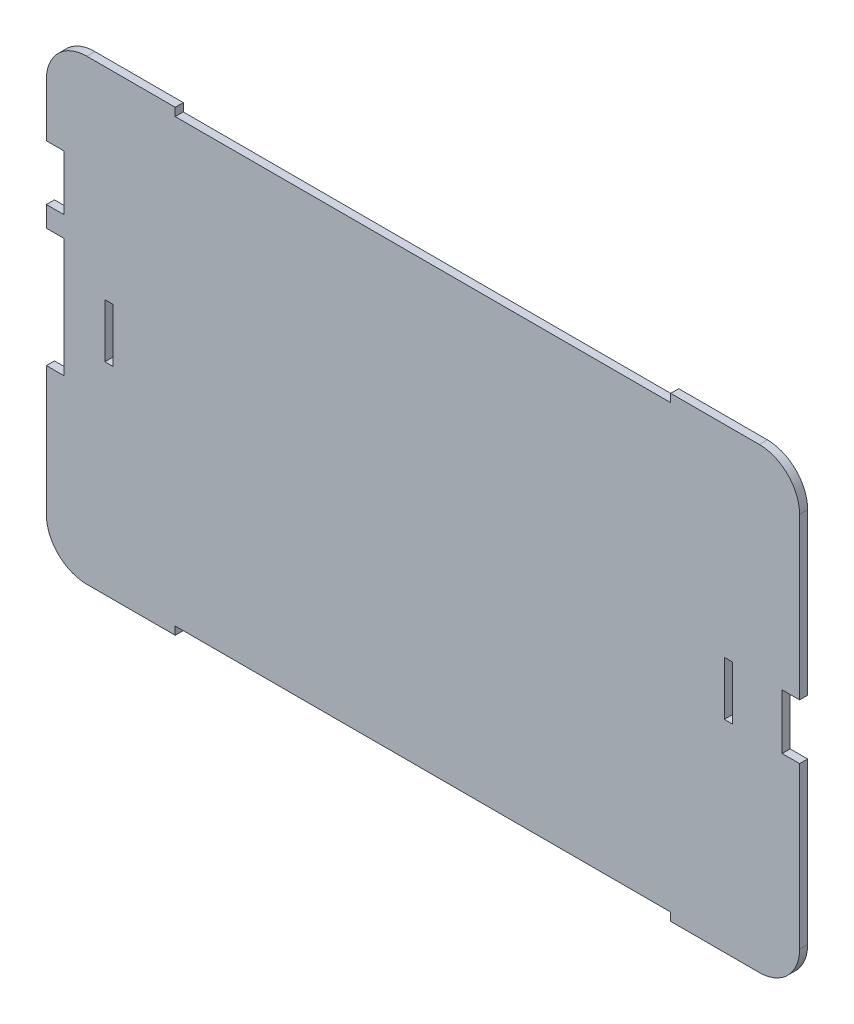
SolidWorks part; units mm, degrees
ref_plane "Alzado" through (0, 0, 0) normal (0, 0, 1) x (1, 0, 0)
ref_plane "Planta" through (0, 0, 0) normal (0, 1, 0) x (1, 0, 0)
ref_plane "Vista lateral" through (0, 0, 0) normal (1, 0, 0) x (0, 0, -1)
sketch "Croquis1" plane through (0, 0, 0) normal (0, 0, 1) x (1, 0, 0)
  line L0 (-207.3448, 3) -> (-174.4448, 3)
  line L1 (-174.4448, 3) -> (-174.4448, 0)
  line L2 (-174.4448, 0) -> (9.7552, 0)
  line L3 (9.7552, 0) -> (9.7552, 3)
  line L4 (9.7552, 3) -> (42.6552, 3)
  line L5 (-207.3448, -167) -> (-174.4448, -167)
  line L6 (-174.4448, -167) -> (-174.4448, -164)
  line L7 (-174.4448, -164) -> (9.7552, -164)
  line L8 (9.7552, -164) -> (9.7552, -167)
  line L9 (9.7552, -167) -> (42.6552, -167)
  line L10 (57.6552, -12) -> (57.6552, -152)
  line L11 (-222.3448, -12) -> (-222.3448, -152)
  line L12 (-207.3448, 3) -> (-222.3448, 3) construction
  line L13 (-222.3448, 3) -> (-222.3448, -12) construction
  line L14 (-222.3448, -152) -> (-222.3448, -167) construction
  line L15 (-222.3448, -167) -> (-207.3448, -167) construction
  line L16 (42.6552, 3) -> (57.6552, 3) construction
  line L17 (57.6552, 3) -> (57.6552, -12) construction
  line L18 (57.6552, -152) -> (57.6552, -167) construction
  line L19 (57.6552, -167) -> (42.6552, -167) construction
  arc A0 (-222.3448, -12) -> (-207.3448, 3) centre (-207.3448, -12) cw
  arc A1 (-222.3448, -152) -> (-207.3448, -167) centre (-207.3448, -152) ccw
  arc A2 (42.6552, -167) -> (57.6552, -152) centre (42.6552, -152) ccw
  arc A3 (42.6552, 3) -> (57.6552, -12) centre (42.6552, -12) cw
  dimension "D1" = 184.2
  dimension "D2" = 32.9
  dimension "D3" = 15
  dimension "D4" = 140
  dimension "D5" = 3
extrude "Saliente-Extruir2" add sketch "Croquis1" along normal blind 3
sketch "Croquis2" plane through (0, 0, 3) normal (0, 0, 1) x (1, 0, 0)
  line L0 (-222.3448, -82) -> (-219.0948, -82) construction
  line L1 (-222.3448, -12) -> (-222.3448, -152) construction
  line L3 (-219.0948, -82) -> (-219.0948, -42) construction
  line L4 (-219.0948, -70.4985) -> (-222.3448, -70.4985) construction
  line L5 (57.6552, -82) -> (54.4052, -82) construction
  line L6 (-222.3448, -52.25) -> (-215.8448, -52.25)
  line L7 (-222.3448, -52.25) -> (-222.3448, -31.75)
  line L8 (-222.3448, -31.75) -> (-215.8448, -31.75)
  line L9 (-215.8448, -52.25) -> (-215.8448, -31.75)
  line L10 (-222.3448, -52.25) -> (-215.8448, -31.75) construction
  line L11 (-222.3448, -31.75) -> (-215.8448, -52.25) construction
  line L12 (-215.8448, -104.1) -> (-222.3448, -104.1)
  line L13 (-215.8448, -104.1) -> (-215.8448, -59.9)
  line L14 (-215.8448, -59.9) -> (-222.3448, -59.9)
  line L15 (-222.3448, -104.1) -> (-222.3448, -59.9)
  line L16 (-215.8448, -104.1) -> (-222.3448, -59.9) construction
  line L17 (-215.8448, -59.9) -> (-222.3448, -104.1) construction
  line L18 (57.6552, -152) -> (57.6552, -12) construction
  line L19 (-219.0948, -82) -> (-199.0948, -82) construction
  line L20 (57.6552, -92.25) -> (51.1552, -92.25)
  line L21 (57.6552, -92.25) -> (57.6552, -71.75)
  line L22 (57.6552, -71.75) -> (51.1552, -71.75)
  line L23 (51.1552, -92.25) -> (51.1552, -71.75)
  line L24 (57.6552, -92.25) -> (51.1552, -71.75) construction
  line L25 (57.6552, -71.75) -> (51.1552, -92.25) construction
  line L26 (51.1552, -82) -> (31.1552, -82) construction
  line L28 (-197.5948, -92) -> (-200.5948, -92)
  line L29 (-197.5948, -92) -> (-197.5948, -72)
  line L30 (-197.5948, -72) -> (-200.5948, -72)
  line L31 (-200.5948, -92) -> (-200.5948, -72)
  line L32 (-197.5948, -92) -> (-200.5948, -72) construction
  line L33 (-197.5948, -72) -> (-200.5948, -92) construction
  line L34 (32.6552, -92) -> (29.6552, -92)
  line L35 (32.6552, -92) -> (32.6552, -72)
  line L36 (32.6552, -72) -> (29.6552, -72)
  line L37 (29.6552, -92) -> (29.6552, -72)
  line L38 (32.6552, -92) -> (29.6552, -72) construction
  line L39 (32.6552, -72) -> (29.6552, -92) construction
  dimension "D1" = 40
  dimension "D2" = 3.25
  dimension "D3" = 20.5
  dimension "D4" = 44.2
  dimension "D5" = 20
  dimension "D6" = 20
  dimension "D7" = 3
extrude "Cortar-Extruir1" cut sketch "Croquis2" against normal blind 3
